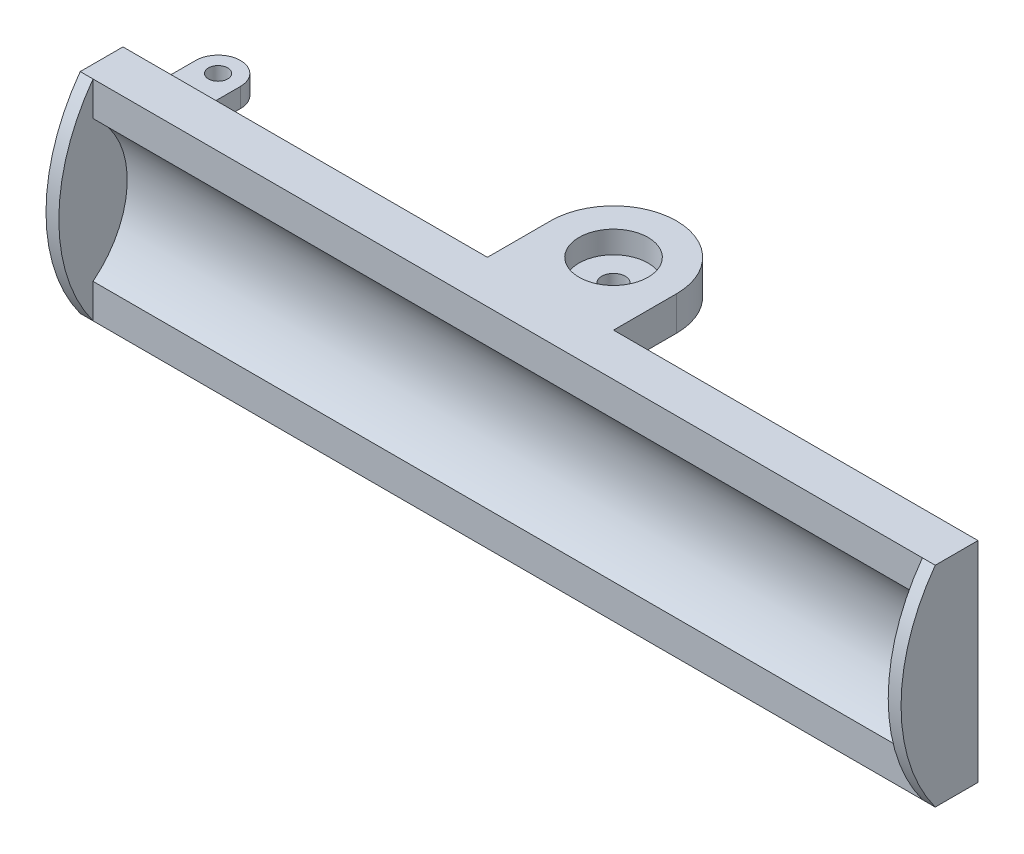
SolidWorks part; units mm, degrees
ref_plane "Front Plane" through (0, 0, 0) normal (1, 0, 0) x (0, 1, 0)
ref_plane "Top Plane" through (0, 0, 0) normal (0, 0, 1) x (0, 1, 0)
ref_plane "Right Plane" through (0, 0, 0) normal (0, 1, 0) x (-1, 0, 0)
sketch "Sketch1" plane through (0, 0, 0) normal (1, 0, 0) x (0, 1, 0)
  line L0 (-5.9881, -2) -> (7.7891, -2) construction
  line L1 (-24.5, -5) -> (24.5, -5)
  line L2 (-24.5, -5) -> (-24.5, 5)
  line L3 (-24.5, 5) -> (24.5, 5)
  line L4 (24.5, -5) -> (24.5, 5)
  line L5 (-24.5, -5) -> (24.5, 5) construction
  line L6 (-24.5, 5) -> (24.5, -5) construction
  circle A0 centre (0, 18) radius 20 construction
  circle A1 centre (0, 18) radius 21
  point P0 (0, 0)
  dimension "D3" = 40
  dimension "D4" = 3
  dimension "D1" = 49
  dimension "D2" = 10
  dimension "D5" = 1
extrude "Boss-Extrude1" add sketch "Sketch1" along normal mid plane 200 contours A1 L3 L2 L1 L4
ref_plane "Midplane Width" through (0, 0, 0) normal (0, -1, 0) x (-1, 0, 0)
sketch "Sketch3" plane through (0, -24.5, 0) normal (0, -1, 0) x (1, 0, 0)
  line L0 (100, -5) -> (-100, -5) construction
  line L1 (-14.75, -19.75) -> (-14.75, -5)
  line L2 (14.75, -19.75) -> (14.75, -5)
  line L3 (-14.75, -5) -> (14.75, -5)
  circle A0 centre (0, -19.75) radius 2.75
  circle A1 centre (0, -19.75) radius 14.75
  line M4 (-100, -5) -> (100, -5)
  dimension "D2" = 12
extrude "Boss-Extrude2" add sketch "Sketch3" against normal blind 8 contours A1 A0 | A1 L1 M4 | A1 L2 L3
sketch "Sketch4" plane through (0, -24.5, 0) normal (0, -1, 0) x (-1, 0, 0)
  circle A0 centre (0, 19.75) radius 8.075
  dimension "D1" = 16.15
extrude "Cut-Extrude1" cut sketch "Sketch4" against normal blind 5.2
sketch "Sketch5" plane through (0, -16.5, 0) normal (0, 1, 0) x (-1, 0, 0)
  circle A0 centre (0, -19.75) radius 2.745
  circle A1 centre (0, -19.75) radius 2.75 construction
  circle A2 centre (0, -19.75) radius 2.75
  dimension "D1" = 5.49
mirror "Mirror1" about plane through (0, 0, 0) normal (0, -1, 0) of "Boss-Extrude2", "Cut-Extrude1"
sketch "Sketch6" plane through (0, 0, 0) normal (0, -1, 0) x (-1, 0, 0)
  line L0 (0, 19.75) -> (92.5, 19.75)
  line L1 (87.25, 19.75) -> (87.25, 5)
  line L2 (14.75, 5) -> (100, 5) construction
  line L3 (97.75, 19.75) -> (97.75, 5)
  line L4 (97.75, 5) -> (87.25, 5)
  circle A0 centre (92.5, 19.75) radius 2.25
  arc A1 (97.75, 19.75) -> (87.25, 19.75) centre (92.5, 19.75) ccw
  circle A2 centre (92.5, 19.75) radius 5.25 construction
  circle A3 centre (0, 19.75) radius 2.745 construction
  circle A4 centre (0, 19.75) radius 2.745
  dimension "D2" = 4.5
  dimension "D1" = 92.5
  dimension "D3" = 3
extrude "Boss-Extrude5" add sketch "Sketch6" along normal blind 4.5 from offset 11
mirror "Mirror2" about plane through (0, 0, 0) normal (0, -1, 0) of "Boss-Extrude5"
sketch "Sketch7" plane through (-100, 0, 0) normal (-1, 0, 0) x (0, -1, 0)
  line L0 (0, 13) -> (-33.9955, 13) construction
  line L1 (-16.4924, 5) -> (16.4924, 5)
  line L5 (-16.4924, 5) -> (-24.5, 5)
  line L6 (-24.5, 5) -> (-24.5, -5)
  line L7 (-24.5, -5) -> (24.5, -5)
  line L8 (24.5, -5) -> (24.5, 5)
  line L9 (24.5, 5) -> (16.4924, 5)
  line L10 (-16.4924, 5) -> (-24.5, 5)
  line L11 (-24.5, 5) -> (-24.5, -5)
  line L12 (-24.5, -5) -> (24.5, -5)
  line L13 (24.5, -5) -> (24.5, 5)
  line L14 (24.5, 5) -> (16.4924, 5)
  arc A0 (24.5, 5) -> (-24.5, 5) centre (0, -28.5156) ccw
  arc A1 (-16.4924, 5) -> (16.4924, 5) centre (0, 18) ccw
  arc A2 (-16.4924, 5) -> (16.4924, 5) centre (0, 18) ccw
  arc M9 (16.4924, 5) -> (-16.4924, 5) centre (0, 18) cw
  line M10 (-16.4924, 5) -> (-24.5, 5)
  line M11 (-24.5, 5) -> (-24.5, -5)
  line M12 (-24.5, -5) -> (24.5, -5)
  line M13 (24.5, -5) -> (24.5, 5)
  line M14 (24.5, 5) -> (16.4924, 5)
  dimension "D2" = 8
  dimension "D1" = 0
extrude "Boss-Extrude6" add sketch "Sketch7" against normal blind 3 contours M14 M9 M10 M11 M12 M13 | L1 M9 | A0 L1 M14 M10
mirror "Mirror3" about plane through (0, 0, 0) normal (1, 0, 0) of "Boss-Extrude6"
